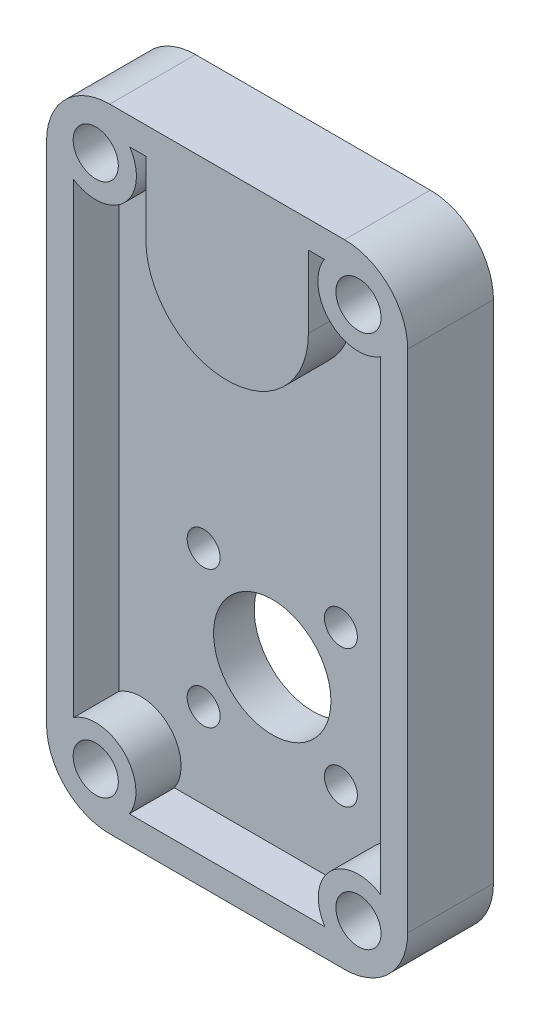
SolidWorks part; units mm, degrees
other "DetailItem1"
ref_plane "Front Plane" through (0, 0, 0) normal (0, 0, 1) x (1, 0, 0)
ref_plane "Top Plane" through (0, 0, 0) normal (0, 1, 0) x (1, 0, 0)
ref_plane "Right Plane" through (0, 0, 0) normal (1, 0, 0) x (0, 0, -1)
sketch "Sketch1" plane through (0, 0, 0) normal (0, 0, 1) x (1, 0, 0)
  line L0 (20, 0) -> (20, 70) construction
  line L1 (0, 0) -> (40, 0)
  line L2 (0, 0) -> (0, 70)
  line L3 (0, 70) -> (40, 70)
  line L4 (40, 0) -> (40, 70)
  line L5 (0, 20) -> (40, 20) construction
  line L6 (12.3986, 27.6014) -> (40, 0) construction
  line L7 (27.6014, 27.6014) -> (0, 0) construction
  circle A0 centre (20, 20) radius 10.75 construction
  circle A2 centre (27.6014, 12.3986) radius 1.825
  circle A3 centre (27.6014, 27.6014) radius 1.825
  circle A4 centre (12.3986, 27.6014) radius 1.825
  circle A5 centre (12.3986, 12.3986) radius 1.825
  circle A6 centre (20, 20) radius 6.5
  dimension "D4" = 21.5
  dimension "D5" = 3.65
  dimension "D6" = 13
  dimension "D1" = 70
  dimension "D2" = 40
  dimension "D3" = 20
extrude "Boss-Extrude1" add sketch "Sketch1" along normal blind 4.5
sketch "Sketch3" plane through (0, 0, 4.5) normal (0, 0, 1) x (1, 0, 0)
  line L0 (0, 0) -> (40, 0) construction
  line L1 (40, 0) -> (40, 70) construction
  line L2 (40, 70) -> (0, 70) construction
  line L3 (0, 70) -> (0, 0) construction
  line L4 (0, 0) -> (40, 0)
  line L5 (40, 0) -> (40, 70)
  line L6 (40, 70) -> (0, 70)
  line L7 (0, 70) -> (0, 0)
  line L8 (9.1648, 3) -> (30.8352, 3)
  line L9 (37, 9.1648) -> (37, 60.7754)
  line L10 (30.7754, 67) -> (29, 67)
  line L11 (3, 60.7754) -> (3, 9.1648)
  line L12 (20, 70) -> (20, 0) construction
  line L13 (3, 59) -> (37, 59) construction
  line L14 (11, 59) -> (11, 67)
  line L15 (29, 59) -> (29, 67)
  line L16 (11, 67) -> (9.2246, 67)
  line L17 (37, 67) -> (3, 67) construction
  line L18 (3, 67) -> (3, 3) construction
  line L19 (37, 3) -> (37, 67) construction
  line L20 (3, 3) -> (37, 3) construction
  circle A0 centre (20, 59) radius 7 construction
  arc A1 (11, 59) -> (29, 59) centre (20, 59) ccw
  circle A2 centre (20, 59) radius 9 construction
  circle A3 centre (5.45, 64.55) radius 2.45 construction
  arc A4 (3, 60.7754) -> (9.2246, 67) centre (5.45, 64.55) ccw
  arc A8 (9.1648, 3) -> (3, 9.1648) centre (5.45, 5.45) ccw
  arc A9 (30.8352, 3) -> (37, 9.1648) centre (34.55, 5.45) cw
  arc A10 (37, 60.7754) -> (30.7754, 67) centre (34.55, 64.55) cw
  dimension "D3" = 14
  dimension "D5" = 4.9
  dimension "D6" = 9
  dimension "D2" = 11
  dimension "D1" = 3
  dimension "D4" = 2
extrude "Boss-Extrude2" add sketch "Sketch3" along normal blind 5
sketch "Sketch6" plane through (0, 0, 9.5) normal (0, 0, 1) x (1, 0, 0)
  arc A0 (9.1648, 3) -> (3, 9.1648) centre (5.45, 5.45) ccw construction
  arc A1 (37, 9.1648) -> (30.8352, 3) centre (34.55, 5.45) ccw construction
  arc A2 (30.7754, 67) -> (37, 60.7754) centre (34.55, 64.55) ccw construction
  arc A3 (3, 60.7754) -> (9.2246, 67) centre (5.45, 64.55) ccw construction
  arc A4 (9.1648, 3) -> (3, 9.1648) centre (5.45, 5.45) ccw construction
  arc A5 (37, 9.1648) -> (30.8352, 3) centre (34.55, 5.45) ccw construction
  arc A6 (30.7754, 67) -> (37, 60.7754) centre (34.55, 64.55) ccw construction
  arc A7 (3, 60.7754) -> (9.2246, 67) centre (5.45, 64.55) ccw construction
  circle A8 centre (5.45, 64.55) radius 2.5
  circle A9 centre (5.45, 5.45) radius 2.5
  circle A10 centre (34.55, 5.45) radius 2.5
  circle A11 centre (34.55, 64.55) radius 2.5
  dimension "D1" = 5
extrude "Cut-Extrude3" cut sketch "Sketch6" against normal blind 7
ref_plane "Mid Plane - Length" through (20, 0, 0) normal (1, 0, 0) x (0, 0, -1)
ref_plane "Mid Plane - Width" through (0, 35, 0) normal (0, -1, 0) x (-1, 0, 0)
sketch "Sketch4" plane through (0, 0, 0) normal (0, 0, -1) x (-1, 0, 0)
  line L0 (-20, 70) -> (-20, 0) construction
  line L1 (-40, 70) -> (0, 70) construction
  line L2 (0, 0) -> (-40, 0) construction
  line L3 (-40, 66) -> (0, 66) construction
  line L4 (-40, 0) -> (-40, 70) construction
  line L5 (0, 70) -> (0, 0) construction
  line L6 (-40, 59) -> (0, 59) construction
  circle A0 centre (-20, 59) radius 7
  dimension "D3" = 14
  dimension "D1" = 4
  dimension "D2" = 7
extrude "Cut-Extrude1" cut sketch "Sketch4" against normal offset from surface (7.5 mm away) 2 up to face at (37.05, 64.55, 9.5)
sketch "Sketch5" plane through (0, 0, 0) normal (0, 0, -1) x (-1, 0, 0)
  line L0 (-20, 70) -> (-20, 39.0054) construction
  line L1 (-40, 70) -> (0, 70) construction
  arc A0 (-7.5811, 47.3088) -> (-32.9371, 47.0672) centre (-20, 20) ccw construction
  text T0 "4108" font "Century Gothic" height 6.25
  dimension "D1" = 50
extrude "Text-4108" cut sketch "Sketch5" against normal blind 1
fillet "Fillet1" radius 7 4 edges at (40, 70, 4.75) (0, 70, 4.75) (0, 0, 4.75) (40, 0, 4.75)
